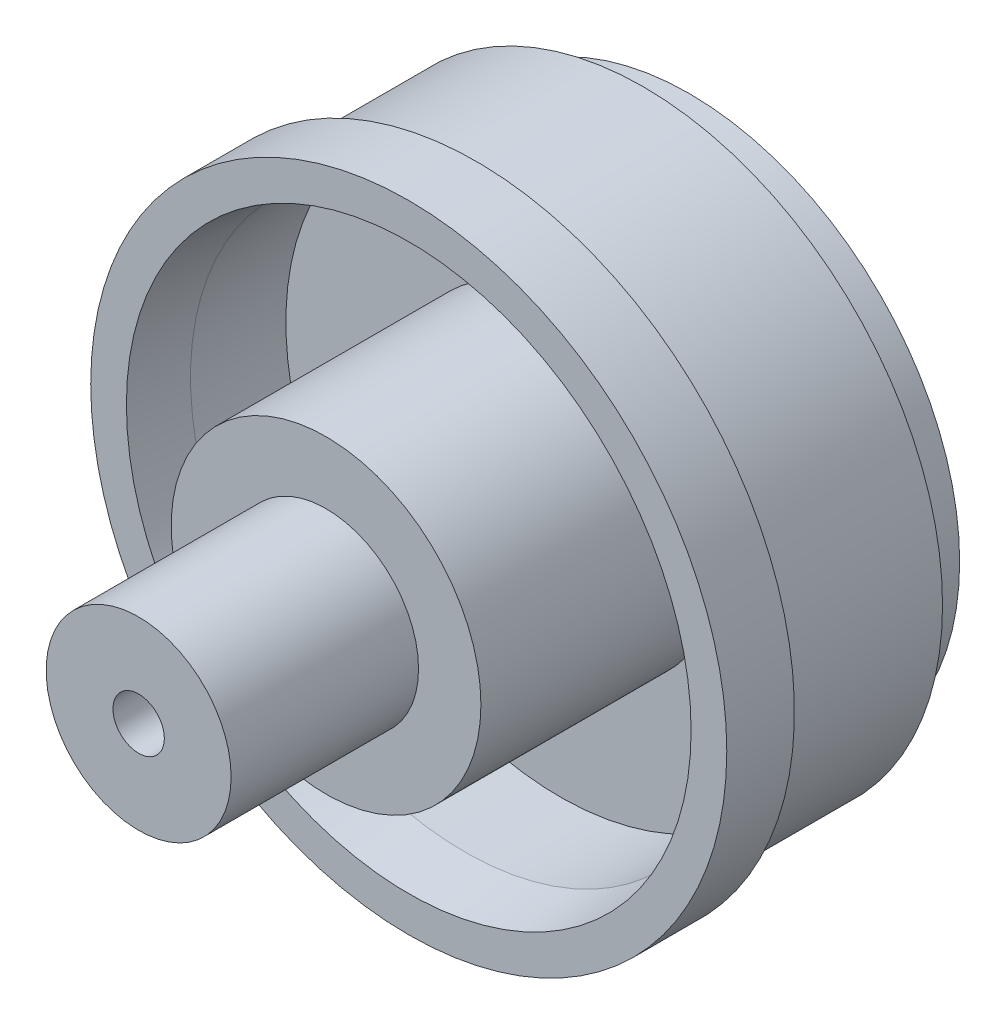
SolidWorks part; units mm, degrees
ref_plane "Front Plane" through (0, 0, 0) normal (0, 0, 1) x (1, 0, 0)
ref_plane "Top Plane" through (0, 0, 0) normal (0, 1, 0) x (1, 0, 0)
ref_plane "Right Plane" through (0, 0, 0) normal (1, 0, 0) x (0, 0, -1)
sketch "Sketch1" plane through (0, 0, 0) normal (0, 0, 1) x (1, 0, 0)
  circle A0 centre (0, 0) radius 49.1363
  dimension "D1" = 98.2726
extrude "Extrude1" add sketch "Sketch1" along normal blind 85.09
sketch "Sketch5" plane through (0, 0, 85.09) normal (0, 0, 1) x (1, 0, 0)
  circle A0 centre (0, 0) radius 3.9688
extrude "Extrude5" cut sketch "Sketch5" against normal blind 26.67
sketch "Sketch2" plane through (0, 0, 85.09) normal (0, 0, 1) x (1, 0, 0)
  circle A0 centre (0, 0) radius 14.2875
  dimension "D1" = 28.575
extrude "Extrude2" cut sketch "Sketch2" against normal blind 28.956 flip side to cut
sketch "Sketch3" plane through (0, 0, 56.134) normal (0, 0, 1) x (1, 0, 0)
  circle A0 centre (0, 0) radius 23.9268
  dimension "D1" = 47.8536
extrude "Extrude3" cut sketch "Sketch3" against normal blind 12.7762 flip side to cut
sketch "Sketch4" plane through (0, 0, 0) normal (0, 0, -1) x (-1, 0, 0)
  circle A0 centre (0, 0) radius 46.228
extrude "Extrude4" cut sketch "Sketch4" against normal blind 32.9057 flip side to cut
sketch "Sketch6" plane through (0, 0, 43.3578) normal (0, 0, 1) x (1, 0, 0)
  circle A0 centre (0, 0) radius 42.3545
  circle A1 centre (0, 0) radius 23.9268
  dimension "D1" = 47.8536
  dimension "D2" = 84.709
extrude "Extrude8" cut sketch "Sketch6" against normal blind 23.368
sketch "Sketch7" plane through (0, 0, 0) normal (0, 0, -1) x (-1, 0, 0)
  circle A0 centre (0, 0) radius 19.177
  dimension "D1" = 38.354
extrude "Extrude9" cut sketch "Sketch7" against normal blind 50.8
sketch "Sketch8" plane through (0, 0, 0) normal (0, 0, -1) x (-1, 0, 0)
  circle A0 centre (0, 0) radius 41.7576
  dimension "D1" = 83.5152
extrude "Extrude10" cut sketch "Sketch8" against normal blind 7.112 flip side to cut
chamfer "Chamfer1" distance 1.27 distance2 8.636 1 edges at (42.3545, 0, 43.3578)
